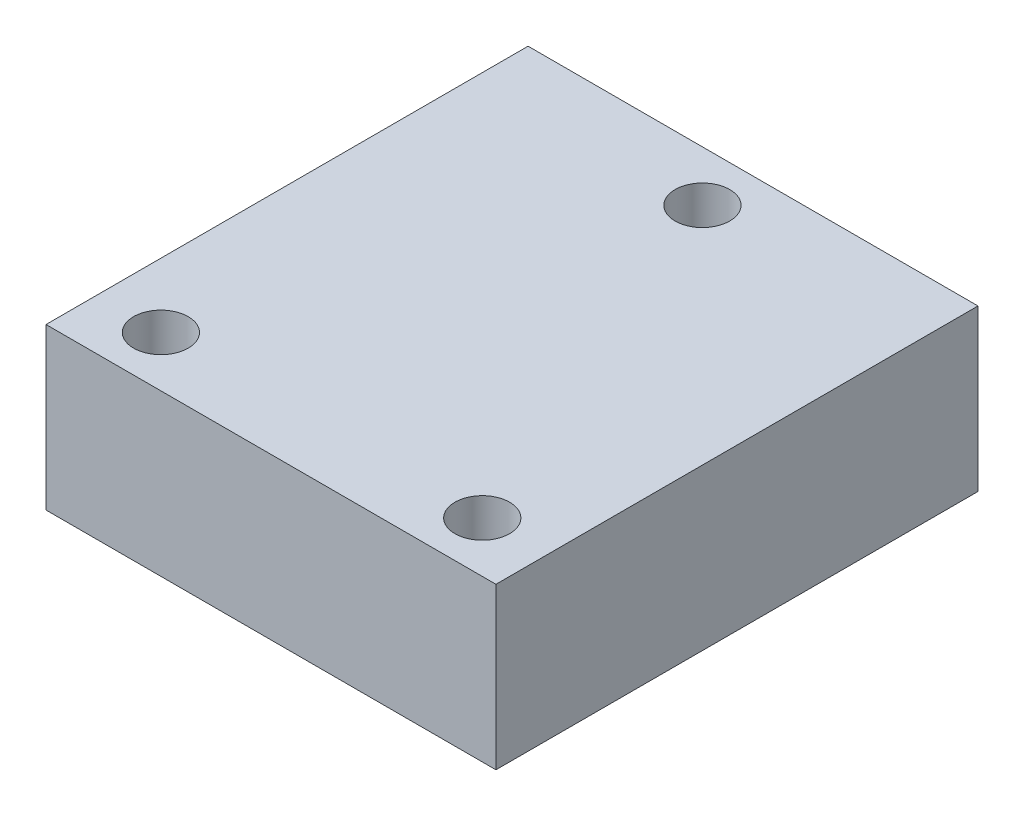
SolidWorks part; units mm, degrees
ref_plane "前视基准面" through (0, 0, 0) normal (0, 0, 1) x (1, 0, 0)
ref_plane "上视基准面" through (0, 0, 0) normal (0, 1, 0) x (1, 0, 0)
ref_plane "右视基准面" through (0, 0, 0) normal (1, 0, 0) x (0, 0, -1)
sketch "草图1" plane through (0, 0, 0) normal (0, 1, 0) x (1, 0, 0)
  line L1 (-14, 15) -> (14, 15)
  line L2 (-14, 15) -> (-14, -15)
  line L3 (-14, -15) -> (14, -15)
  line L4 (14, 15) -> (14, -15)
  line L5 (-14, 15) -> (14, -15) construction
  line L6 (-14, -15) -> (14, 15) construction
  point P0 (0, 0)
  dimension "D1" = 28
  dimension "D2" = 30
extrude "凸台-拉伸1" add sketch "草图1" along normal blind 10
sketch "草图2" plane through (0, 10, 0) normal (0, 1, 0) x (1, 0, 0)
  line L0 (0, 11.85) -> (0, -11.85) construction
  line L1 (-10, -11.85) -> (10, -11.85) construction
  circle A0 centre (0, 11.85) radius 1.7
  circle A1 centre (-10, -11.85) radius 1.7
  circle A2 centre (10, -11.85) radius 1.7
  point P4 (0, 0)
  point P8 (0, -11.85)
  dimension "D3" = 3.4
  dimension "D1" = 23.7
  dimension "D2" = 20
extrude "切除-拉伸1" cut sketch "草图2" against normal through all
